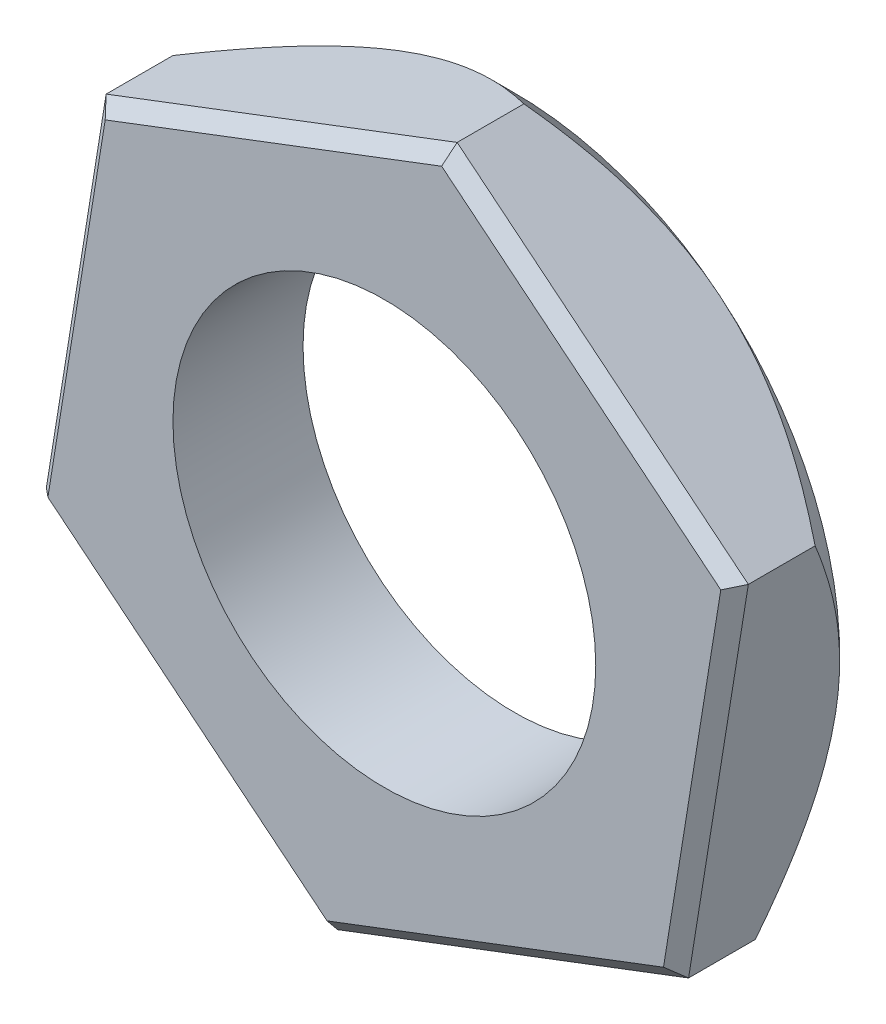
SolidWorks part; units mm, degrees
ref_plane "Alzado" through (0, 0, 0) normal (0, 0, 1) x (1, 0, 0)
ref_plane "Planta" through (0, 0, 0) normal (0, 1, 0) x (1, 0, 0)
ref_plane "Vista lateral" through (0, 0, 0) normal (1, 0, 0) x (0, 0, -1)
sketch "Croquis1" plane through (0, 0, 0) normal (0, 0, 1) x (1, 0, 0)
  line L1 (-5.3957, -2.0543) -> (-0.9188, -5.6999)
  line L2 (-0.9188, -5.6999) -> (4.4769, -3.6457)
  line L3 (4.4769, -3.6457) -> (5.3957, 2.0543)
  line L4 (5.3957, 2.0543) -> (0.9188, 5.6999)
  line L5 (0.9188, 5.6999) -> (-4.4769, 3.6457)
  line L6 (-4.4769, 3.6457) -> (-5.3957, -2.0543)
  circle A0 centre (0, 0) radius 5 construction
  circle A1 centre (0, 0) radius 3.25
  dimension "D1" = 10
  dimension "D2" = 6.5
extrude "Saliente-Extruir1" add sketch "Croquis1" along normal blind 2
sketch "Croquis2" plane through (0, 0, 0) normal (0, 0, -1) x (-1, 0, 0)
  circle A0 centre (0, 0) radius 5
extrude "Cortar-Extruir1" cut sketch "Croquis2" against normal blind 1 draft 45 flip side to cut
chamfer "Chaflán2" distance 0.2 angle 46 6 edges at (1.7791, -4.6728, 2) (4.9363, -0.7957, 2) (3.1572, 3.8771, 2) (-3.1572, -3.8771, 2) (-4.9363, 0.7957, 2) (-1.7791, 4.6728, 2)
